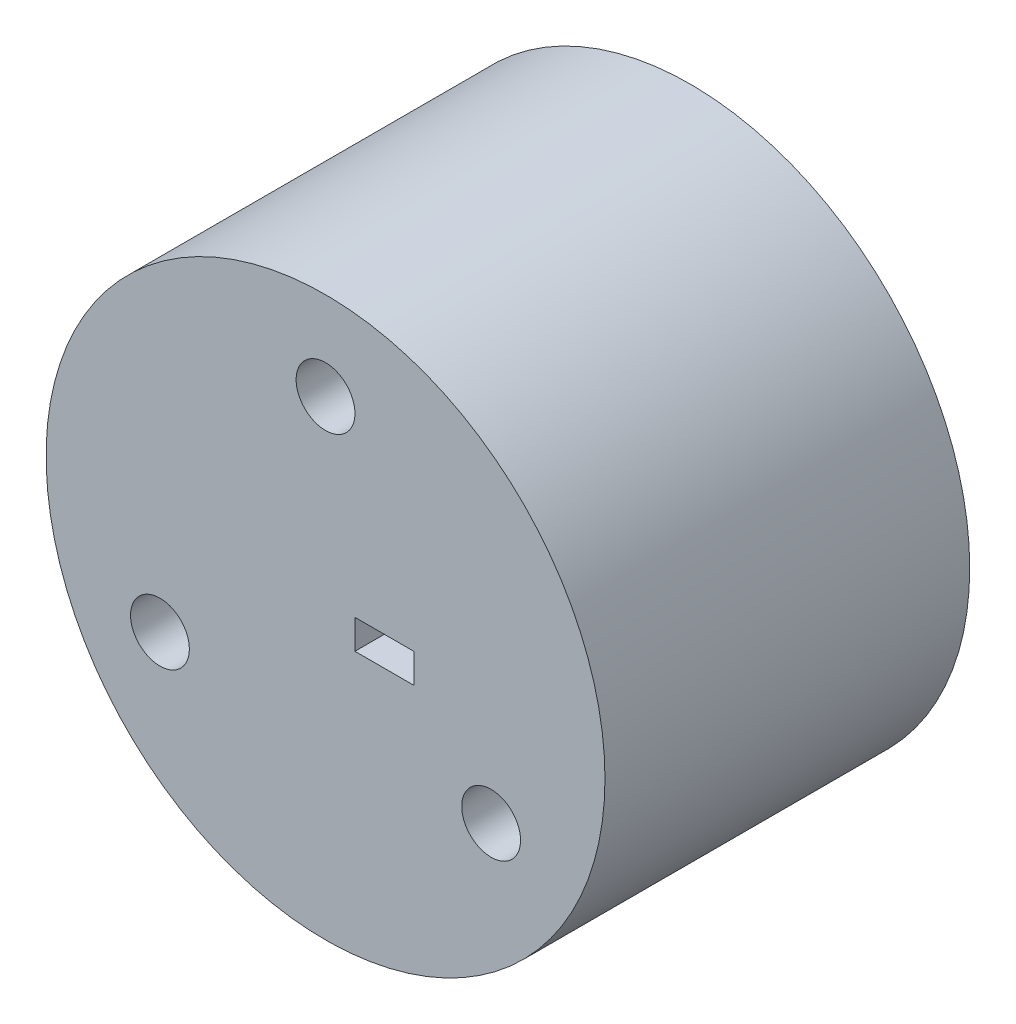
SolidWorks part; units mm, degrees
ref_plane "Front Plane" through (0, 0, 0) normal (0, 0, 1) x (1, 0, 0)
ref_plane "Top Plane" through (0, 0, 0) normal (0, 1, 0) x (1, 0, 0)
ref_plane "Right Plane" through (0, 0, 0) normal (1, 0, 0) x (0, 0, -1)
sketch "Sketch1" plane through (0, 0, 0) normal (0, 0, 1) x (1, 0, 0)
  circle A0 centre (0, 0) radius 47.5
  dimension "D1" = 95
extrude "Boss-Extrude1" add sketch "Sketch1" along normal blind 62
sketch "Sketch2" plane through (0, 0, 62) normal (0, 0, 1) x (1, 0, 0)
  line L1 (5, 2.5) -> (15, 2.5)
  line L2 (5, 2.5) -> (5, -2.5)
  line L3 (5, -2.5) -> (15, -2.5)
  line L4 (15, 2.5) -> (15, -2.5)
  line L5 (5, 2.5) -> (15, -2.5) construction
  line L6 (5, -2.5) -> (15, 2.5) construction
  circle A0 centre (0, 0) radius 10 construction
  point P3 (10, 0)
  dimension "D1" = 20
  dimension "D2" = 5
  dimension "D3" = 10
extrude "Cut-Extrude1" cut sketch "Sketch2" against normal blind 20
sketch "Sketch3" plane through (0, 0, 62) normal (0, 0, 1) x (1, 0, 0)
  circle A0 centre (0, 0) radius 32.5 construction
  circle A1 centre (0, 32.5) radius 5
  circle A2 centre (28.1458, -16.25) radius 5
  circle A3 centre (-28.1458, -16.25) radius 5
  point P12 (0, 0)
  dimension "1" = 10
  dimension "D2" = 65
  dimension "D3" = 3
extrude "Cut-Extrude2" cut sketch "Sketch3" against normal through all
